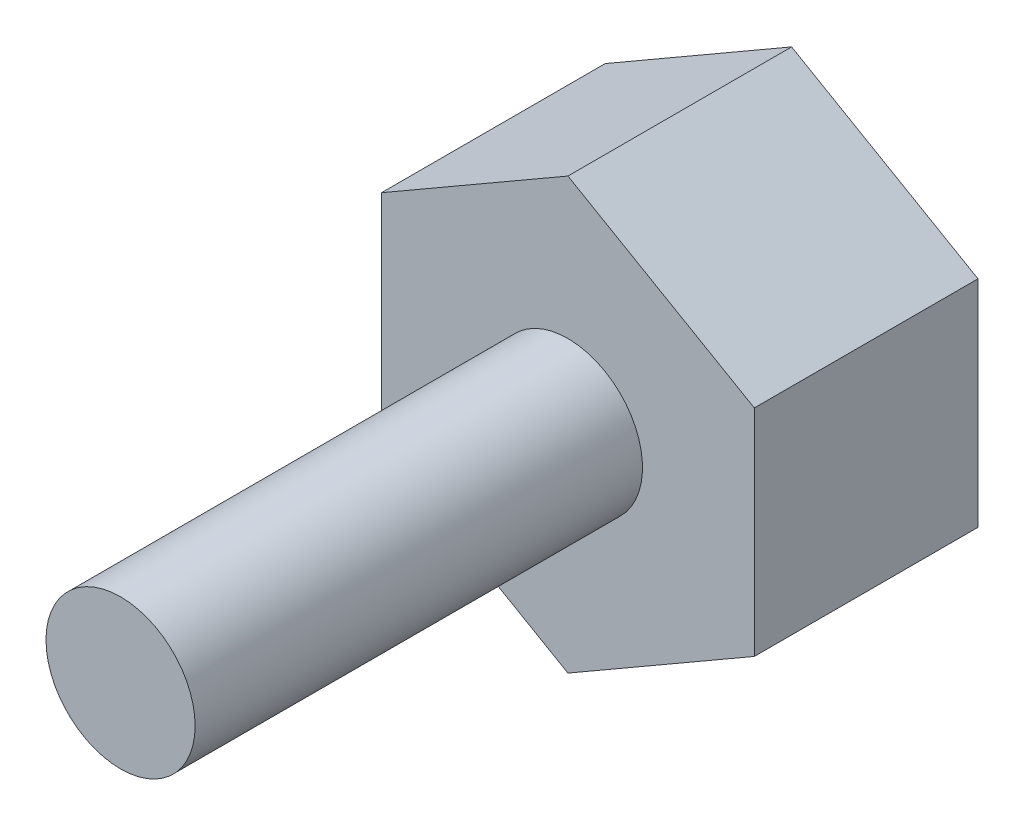
SolidWorks part; units mm, degrees
ref_plane "Front Plane" through (0, 0, 0) normal (0, 0, 1) x (1, 0, 0)
ref_plane "Top Plane" through (0, 0, 0) normal (0, 1, 0) x (1, 0, 0)
ref_plane "Right Plane" through (0, 0, 0) normal (1, 0, 0) x (0, 0, -1)
sketch "Sketch1" plane through (0, 0, 0) normal (0, 0, 1) x (1, 0, 0)
  circle A0 centre (-63.4948, 14.9787) radius 1
extrude "Boss-Extrude1" add sketch "Sketch1" along normal blind 6
sketch "Sketch2" plane through (0, 0, 0) normal (0, 0, -1) x (-1, 0, 0)
  line L1 (63.4948, 12.092) -> (65.9948, 13.5353)
  line L2 (65.9948, 13.5353) -> (65.9948, 16.4221)
  line L3 (65.9948, 16.4221) -> (63.4948, 17.8655)
  line L4 (63.4948, 17.8655) -> (60.9948, 16.4221)
  line L5 (60.9948, 16.4221) -> (60.9948, 13.5353)
  line L6 (60.9948, 13.5353) -> (63.4948, 12.092)
  circle A0 centre (63.4948, 14.9787) radius 2.5 construction
  dimension "D1" = 5
extrude "Boss-Extrude2" add sketch "Sketch2" along normal blind 3
